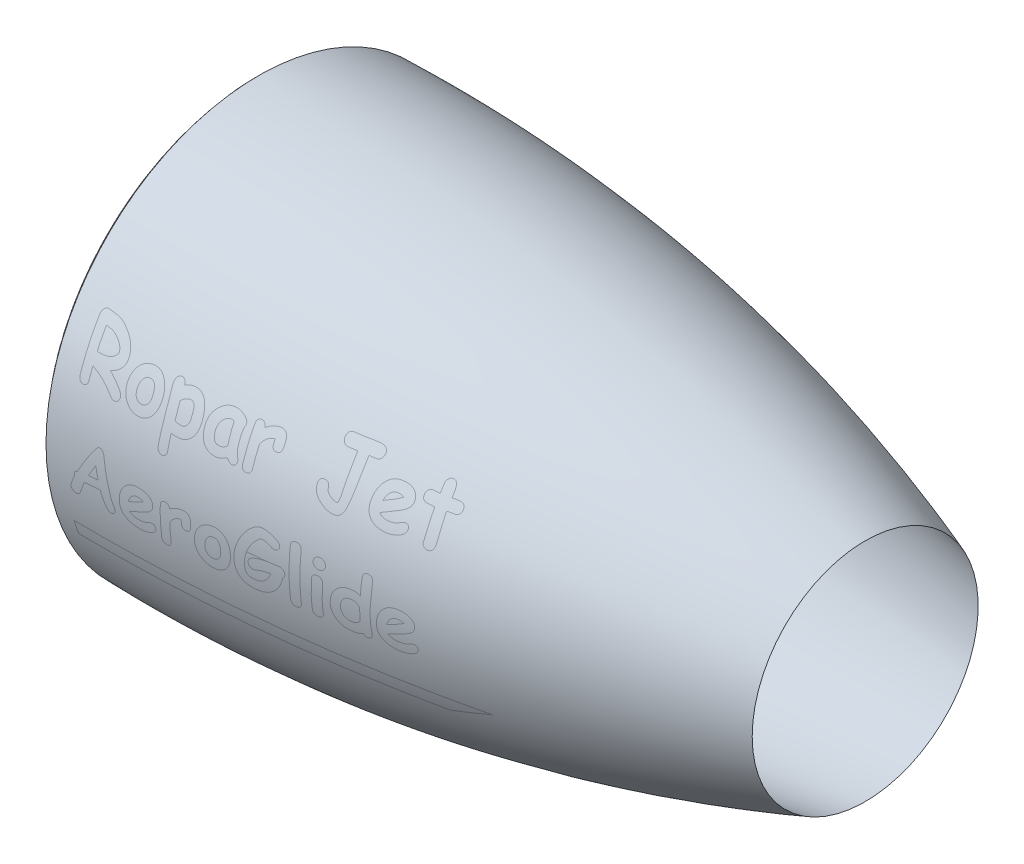
SolidWorks part; units mm, degrees
material "1060 Alloy"
ref_plane "Front Plane" through (0, 0, 0) normal (0, 0, 1) x (1, 0, 0)
ref_plane "Top Plane" through (0, 0, 0) normal (0, 1, 0) x (1, 0, 0)
ref_plane "Right Plane" through (0, 0, 0) normal (1, 0, 0) x (0, 0, -1)
sketch "Sketch1" plane through (0, 0, 0) normal (0, 0, 1) x (1, 0, 0)
  line L0 (0, 0) -> (233.9991, 0) construction
  line L1 (0, 0) -> (0, 203.0229) construction
  line L2 (0, 180) -> (25, 180)
  line L3 (25, 180) -> (32.8623, 190)
  line L4 (32.8623, 190) -> (57.8623, 190)
  line L5 (580, 108) -> (57.8623, 190)
  spline S0 degree 2 poles (0, 203.0229) (299.257, 210.1505) (580, 108) knots 0 0 0 1 1 1
  spline S1 degree 2 poles (0, 203.0229) (-11.7422, 191.6556) (0, 180) knots 0 0 0 1 1 1
  dimension "D1" = 580
  dimension "D2" = 108
  dimension "D3" = 180
  dimension "D4" = 190
  dimension "D5" = 25
  dimension "D6" = 25
sketch "Sketch2" plane through (0, 0, 0) normal (0, 0, 1) x (1, 0, 0)
revolve "Revolve1" add sketch "Sketch1" angle 360 about L0
ref_plane "Plane1" through (0, 0, 250) normal (0, 0, 1) x (1, 0, 0)
sketch "Sketch3" plane through (0, 0, 250) normal (0, 0, 1) x (1, 0, 0)
  line L0 (19.8155, 59.9504) -> (448.1361, 59.9504) construction
  line L1 (19.8155, -26.7249) -> (448.1361, -26.7249) construction
  line L2 (18.5462, -58.3831) -> (379.6192, -58.3831)
  line L3 (18.5462, -58.3831) -> (18.5462, -71.486)
  line L4 (18.5462, -71.486) -> (342.8564, -71.486)
  line L5 (342.8564, -71.486) -> (379.6192, -58.3831)
  text T0 "Ropar Jet" font "Comic Sans MS" height 50
  text T1 "AeroGlide" font "Comic Sans MS" height 50
split line "Split Line1"
